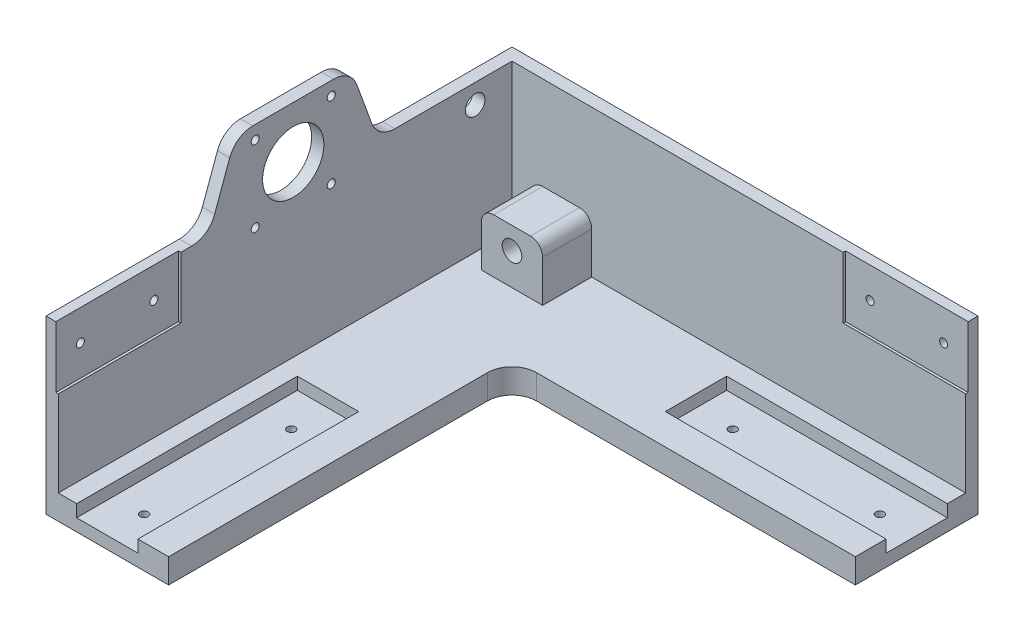
SolidWorks part; units mm, degrees
ref_plane "Front Plane" through (0, 0, 0) normal (0, 0, 1) x (1, 0, 0)
ref_plane "Top Plane" through (0, 0, 0) normal (0, 1, 0) x (1, 0, 0)
ref_plane "Right Plane" through (0, 0, 0) normal (1, 0, 0) x (0, 0, -1)
sketch "Sketch1" plane through (0, 0, 0) normal (0, 1, 0) x (1, 0, 0)
  line L1 (-59.0929, 30.23) -> (130.9071, 30.23)
  line L3 (0.9071, -19.77) -> (130.9071, -19.77)
  line L4 (130.9071, 30.23) -> (130.9071, -19.77)
  line L6 (-59.0929, 30.23) -> (-59.0929, -159.77)
  line L7 (-59.0929, -159.77) -> (-9.0929, -159.77)
  line L8 (-9.0929, -29.77) -> (-9.0929, -159.77)
  arc A0 (0.9071, -19.77) -> (-9.0929, -29.77) centre (0.9071, -29.77) ccw
  dimension "D3" = 10
  dimension "D1" = 50
  dimension "D2" = 190
extrude "Boss-Extrude1" add sketch "Sketch1" along normal blind 10
sketch "Sketch2" plane through (0, 10, 0) normal (0, 1, 0) x (1, 0, 0)
  line L0 (-869.0929, 5.23) -> (49130.9071, 5.23) construction
  line L1 (130.9071, -19.77) -> (130.9071, 30.23) construction
  line L2 (-34.0929, -1159.77) -> (-34.0929, 48840.23) construction
  line L3 (-59.0929, -159.77) -> (-9.0929, -159.77) construction
  line L5 (40.9071, 17.73) -> (130.9071, 17.73)
  line L7 (40.9071, -7.27) -> (130.9071, -7.27)
  line L8 (130.9071, 17.73) -> (130.9071, -7.27)
  line L9 (-46.5929, -159.77) -> (-21.5929, -159.77)
  line L11 (40.9071, 17.73) -> (40.9071, -7.27)
  line L14 (-46.5929, -159.77) -> (-46.5929, -69.77)
  line L16 (-21.5929, -159.77) -> (-21.5929, -69.77)
  line L17 (-46.5929, -69.77) -> (-21.5929, -69.77)
  point P5 (130.9071, 5.23)
  point P10 (-34.0929, -159.77)
  dimension "D2" = 90
  dimension "D4" = 25
  dimension "D5" = 90
  dimension "D8" = 25
extrude "Cut-Extrude1" cut sketch "Sketch2" against normal blind 5
sketch "Sketch3" plane through (0, 5, 0) normal (0, 1, 0) x (1, 0, 0)
  line L0 (40.9071, 17.73) -> (40.9071, -7.27) construction
  line L1 (-21.5929, -69.77) -> (-46.5929, -69.77) construction
  line L4 (-200869.0929, 5.23) -> (249130.9071, 5.23) construction
  line L5 (-34.0929, -201159.77) -> (-34.0929, 248840.23) construction
  line L6 (55.9071, -1097.7668) -> (55.9071, 48902.2332) construction
  line L7 (-864.1378, -84.77) -> (49135.8622, -84.77) construction
  line L12 (130.9071, 17.73) -> (130.9071, -7.27) construction
  line L13 (-46.5929, -159.77) -> (-21.5929, -159.77) construction
  circle A0 centre (55.9071, 5.23) radius 1.65
  circle A1 centre (115.9071, 5.23) radius 1.65
  circle A2 centre (-34.0929, -84.77) radius 1.65
  circle A3 centre (-34.0929, -144.77) radius 1.65
  dimension "D1" = 3.3
  dimension "D2" = 15
  dimension "D3" = 15
  dimension "D4" = 15
  dimension "D5" = 15
extrude "Cut-Extrude2" cut sketch "Sketch3" against normal through all
sketch "Sketch4" plane through (0, 10, 0) normal (0, 1, 0) x (1, 0, 0)
  line L0 (130.9071, 30.23) -> (-59.0929, 30.23) construction
  line L1 (-46.5929, 30.23) -> (-21.5929, 30.23)
  line L2 (-46.5929, 30.23) -> (-46.5929, 5.23)
  line L3 (-46.5929, 5.23) -> (-21.5929, 5.23)
  line L4 (-21.5929, 30.23) -> (-21.5929, 5.23)
  line L5 (-34.0929, -1154.4017) -> (-34.0929, 48845.5983) construction
  line L9 (-59.0929, 30.23) -> (-59.0929, -159.77) construction
  dimension "D1" = 25
  dimension "D2" = 25
  dimension "D3" = 12.5
extrude "Boss-Extrude2" add sketch "Sketch4" along normal blind 22
sketch "Sketch5" plane through (0, 0, -30.23) normal (0, 0, -1) x (-1, 0, 0)
  line L2 (34.0929, -975) -> (34.0929, 49025) construction
  line L3 (21.5929, 32) -> (46.5929, 32) construction
  line L4 (46.5929, 10) -> (59.0929, 10) construction
  circle A0 centre (34.0929, 23) radius 4
  point P11 (34.0929, 32)
  dimension "D1" = 8
  dimension "D2" = 13
extrude "Cut-Extrude3" cut sketch "Sketch5" against normal through all
fillet "Fillet1" radius 5 2 edges at (-46.5929, 32, -17.73) (-21.5929, 32, -17.73)
sketch "Sketch6" plane through (-59.0929, 0, 0) normal (-1, 0, 0) x (0, 0, 1)
  line L1 (-30.23, 10) -> (159.77, 10)
  line L2 (-30.23, 10) -> (-30.23, 100)
  line L3 (-30.23, 100) -> (159.77, 100)
  line L4 (159.77, 10) -> (159.77, 100)
  dimension "D1" = 90
extrude "Boss-Extrude3" add sketch "Sketch6" against normal blind 5
sketch "Sketch7" plane through (-54.0929, 0, 0) normal (1, 0, 0) x (0, 0, -1)
  line L0 (-1200.0052, 51) -> (48799.9948, 51) construction
  line L1 (30.23, 10) -> (-159.77, 10) construction
  line L2 (30.23, 100) -> (30.23, 10) construction
  line L3 (-63.971, 100) -> (-63.971, 58) construction
  line L4 (-84.971, 100) -> (-42.971, 100) construction
  line L5 (-84.971, 100) -> (-84.971, 58) construction
  line L6 (-84.971, 58) -> (-42.971, 58) construction
  line L7 (-42.971, 100) -> (-42.971, 58) construction
  line L8 (-84.971, 79) -> (-42.971, 79) construction
  circle A0 centre (10.23, 62) radius 11 construction
  circle A1 centre (10.23, 62) radius 4
  circle A2 centre (-63.971, 79) radius 12.5
  circle A3 centre (-79.471, 94.5) radius 1.65
  circle A4 centre (-48.471, 94.5) radius 1.65
  circle A5 centre (-48.471, 63.5) radius 1.65
  circle A6 centre (-79.471, 63.5) radius 1.65
  dimension "D2" = 9
  dimension "D3" = 22
  dimension "D4" = 8
  dimension "D6" = 25
  dimension "D7" = 3.3
  dimension "D8" = 31
  dimension "D1" = 41
  dimension "D5" = 42
  dimension "D9" = 31
  dimension "D10" = 7
extrude "Cut-Extrude4" cut sketch "Sketch7" against normal through all
sketch "Sketch8" plane through (0, 10, 0) normal (0, 1, 0) x (1, 0, 0)
  line L1 (-54.0929, 30.23) -> (130.9071, 30.23)
  line L2 (-54.0929, 30.23) -> (-54.0929, 25.23)
  line L3 (-54.0929, 25.23) -> (130.9071, 25.23)
  line L4 (130.9071, 30.23) -> (130.9071, 25.23)
  dimension "D1" = 5
extrude "Boss-Extrude4" add sketch "Sketch8" along normal blind 60
sketch "Sketch9" plane through (0, 0, -30.23) normal (0, 0, -1) x (-1, 0, 0)
  circle A0 centre (34.0929, 23) radius 4
  circle A1 centre (34.0929, 23) radius 4 construction
extrude "Cut-Extrude5" cut sketch "Sketch9" against normal through all
sketch "Sketch10" plane through (-54.0929, 0, 0) normal (1, 0, 0) x (0, 0, -1)
  line L0 (-159.77, 70) -> (-98.3901, 70)
  line L1 (-159.77, 10) -> (-159.77, 100) construction
  line L2 (-98.3901, 70) -> (-87.471, 100)
  line L3 (-159.77, 100) -> (30.23, 100) construction
  line L4 (-40.471, 100) -> (-29.5519, 70)
  line L5 (-87.471, 100) -> (-159.77, 100)
  line L6 (-29.5519, 70) -> (25.23, 70)
  line L7 (25.23, 70) -> (30.23, 70)
  line L8 (30.23, 70) -> (30.23, 100)
  line L9 (30.23, 100) -> (-40.471, 100)
  line L10 (-159.77, 100) -> (-159.77, 70)
  circle A0 centre (-79.471, 94.5) radius 1.65 construction
  circle A1 centre (-48.471, 94.5) radius 1.65 construction
  dimension "D1" = 8
  dimension "D2" = 8
  dimension "D3" = 110
  dimension "D4" = 110
extrude "Cut-Extrude6" cut sketch "Sketch10" against normal through all
fillet "Fillet2" radius 10 4 edges at (-56.5929, 70, 98.3901) (-56.5929, 100, 87.471) (-56.5929, 100, 40.471) (-56.5929, 70, 29.5519)
sketch "Sketch11" plane through (0, 0, -25.23) normal (0, 0, 1) x (1, 0, 0)
  line L0 (-54.0929, 70) -> (130.9071, 70) construction
  line L1 (80.9071, 70) -> (130.9071, 70)
  line L2 (80.9071, 70) -> (80.9071, 45)
  line L3 (80.9071, 45) -> (130.9071, 45)
  line L4 (130.9071, 70) -> (130.9071, 45)
  line L5 (130.9071, 70) -> (130.9071, 10) construction
  dimension "D1" = 25
  dimension "D2" = 50
extrude "Cut-Extrude7" cut sketch "Sketch11" against normal blind 1
sketch "Sketch12" plane through (0, 0, -26.23) normal (0, 0, 1) x (1, 0, 0)
  line L0 (-959.0929, 57.5) -> (49040.9071, 57.5) construction
  line L1 (80.9071, 70) -> (80.9071, 45) construction
  line L3 (80.9071, 70) -> (80.9071, 45) construction
  line L4 (130.9071, 70) -> (130.9071, 0) construction
  circle A0 centre (90.9071, 57.5) radius 1.65
  circle A1 centre (120.9071, 57.5) radius 1.65
  point P9 (80.9071, 57.5)
  dimension "D1" = 3.3
  dimension "D2" = 10
  dimension "D3" = 10
extrude "Cut-Extrude8" cut sketch "Sketch12" against normal through all
sketch "Sketch13" plane through (-54.0929, 0, 0) normal (1, 0, 0) x (0, 0, -1)
  line L1 (-159.77, 70) -> (-109.77, 70)
  line L2 (-159.77, 70) -> (-159.77, 45)
  line L3 (-159.77, 45) -> (-109.77, 45)
  line L4 (-109.77, 70) -> (-109.77, 45)
  dimension "D1" = 50
  dimension "D2" = 25
extrude "Cut-Extrude9" cut sketch "Sketch13" against normal blind 1
sketch "Sketch14" plane through (-55.0929, 0, 0) normal (1, 0, 0) x (0, 0, -1)
  line L0 (-1159.77, 57.5) -> (48840.23, 57.5) construction
  line L1 (-159.77, 70) -> (-159.77, 45) construction
  line L2 (-109.77, 45) -> (-109.77, 70) construction
  circle A0 centre (-149.77, 57.5) radius 1.65
  circle A1 centre (-119.77, 57.5) radius 1.65
  point P9 (-159.77, 57.5)
  dimension "D1" = 3.3
  dimension "D2" = 10
  dimension "D3" = 10
extrude "Cut-Extrude10" cut sketch "Sketch14" against normal through all
